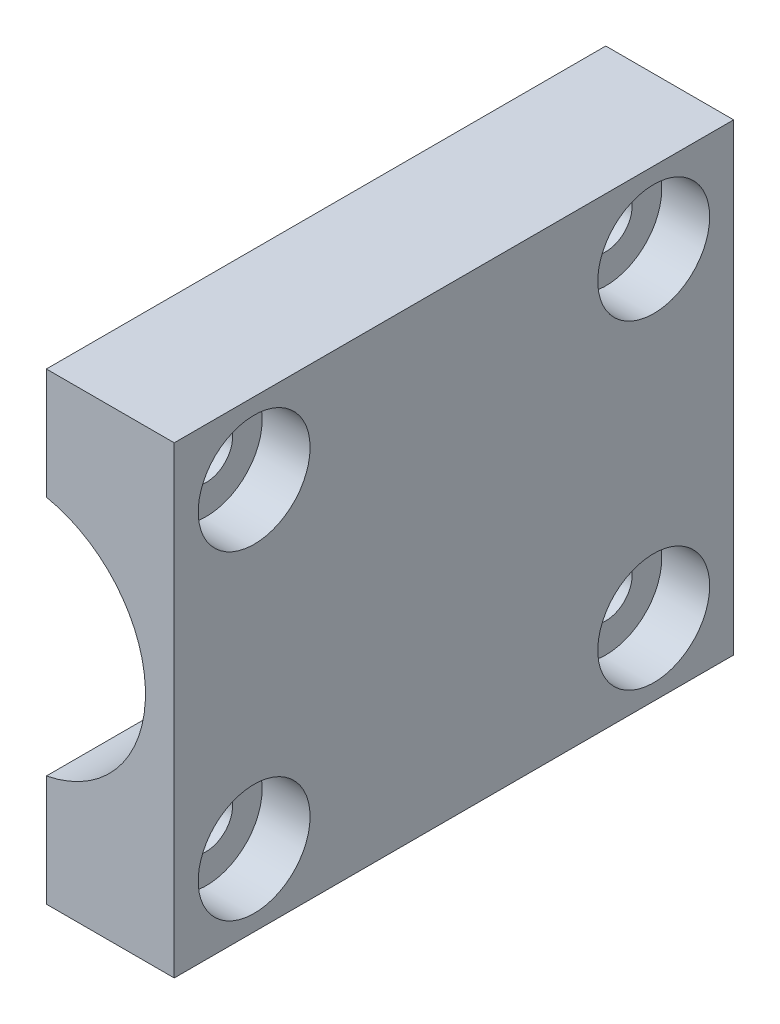
SolidWorks part; units mm, degrees
ref_plane "Plano frontal" through (0, 0, 0) normal (0, 0, 1) x (1, 0, 0)
ref_plane "Plano superior" through (0, 0, 0) normal (0, 1, 0) x (1, 0, 0)
ref_plane "Plano direito" through (0, 0, 0) normal (1, 0, 0) x (0, 0, -1)
sketch "Esboço2" plane through (0, 0, 0) normal (0, 0, 1) x (1, 0, 0)
  line L0 (-9.5, 15) -> (-9.5, 32.5)
  line L1 (-9.5, -32.5) -> (9.5, -32.5)
  line L2 (-9.5, -32.5) -> (-9.5, -15)
  line L3 (-9.5, 32.5) -> (9.5, 32.5)
  line L4 (9.5, -32.5) -> (9.5, 32.5)
  line L5 (-9.5, -32.5) -> (9.5, 32.5) construction
  line L6 (-9.5, 32.5) -> (9.5, -32.5) construction
  line L7 (-36.5, 15) -> (-9.5, 15)
  line L8 (-36.5, 15) -> (-36.5, 12)
  line L9 (-25, -15) -> (-9.5, -15)
  line L10 (0, 0) -> (-50.7474, 0) construction
  line L11 (-36.5, 15) -> (-9.5, -15) construction
  line L12 (-36.5, -15) -> (-9.5, 15) construction
  line L13 (-16, 2) -> (-9, 2)
  line L14 (-16, 2) -> (-16, 12)
  line L15 (-16, 12) -> (-9, 12)
  line L16 (-9, 2) -> (-9, 12)
  line L17 (-16, 2) -> (-9, 12) construction
  line L18 (-16, 12) -> (-9, 2) construction
  line L19 (-20.5, 12) -> (-36.5, 12)
  line L20 (-20.5, 12) -> (-20.5, 2)
  line L21 (-20.5, 2) -> (-36.5, 2)
  line L22 (-36.5, -2) -> (-25, -2)
  line L23 (-20.5, 12) -> (-36.5, 2) construction
  line L24 (-20.5, 2) -> (-36.5, 12) construction
  line L25 (-9, -2) -> (-25, -2)
  line L26 (-9, -2) -> (-9, -12)
  line L27 (-9, -12) -> (-25, -12)
  line L29 (-25, -12) -> (-25, -15)
  line L31 (-36.5, 2) -> (-36.5, -2)
  line L33 (-9, -2) -> (-25, -12) construction
  line L34 (-9, -12) -> (-25, -2) construction
  circle A0 centre (0, 0) radius 7.7
  point P7 (-23, 0)
  point P12 (-12.5, 7)
  point P18 (-28.5, 7)
  point P26 (-17, -7)
  dimension "D1" = 15.4
  dimension "D2" = 65
  dimension "D3" = 19
  dimension "D4" = 30
  dimension "D5" = 27
  dimension "D6" = 3
  dimension "D7" = 7
  dimension "D9" = 16
  dimension "D10" = 0.5
  dimension "D11" = 10
  dimension "D12" = 3
extrude "Ressalto-extrusão1" add sketch "Esboço2" along normal blind 35
sketch "Esboço3" plane through (-9.5, 0, 0) normal (-1, 0, 0) x (0, 0, 1)
  line L0 (0, 0) -> (35, 0) construction
  line L1 (35, 15) -> (0, 15) construction
  line L2 (35, 30.7367) -> (25, 32.5)
  line L3 (35, 32.5) -> (35, 15) construction
  line L4 (17.5, 32.5) -> (17.5, 15) construction
  line L5 (24.7398, 20.1694) -> (30.0578, 19.2317)
  line L6 (24.7398, 20.1694) -> (24.2189, 17.215)
  line L7 (24.2189, 17.215) -> (29.5368, 16.2773)
  line L8 (30.0578, 19.2317) -> (29.5368, 16.2773)
  line L9 (24.7398, 20.1694) -> (29.5368, 16.2773) construction
  line L10 (24.2189, 17.215) -> (30.0578, 19.2317) construction
  line L12 (19.1813, 24.7035) -> (42.7265, 20.5519) construction
  line L13 (21.3215, 23.8185) -> (42.6397, 20.0595)
  line L14 (21.4952, 24.8033) -> (42.8134, 21.0443)
  line L15 (17.5868, 25.4924) -> (42.8134, 21.0443) construction
  line L16 (17.5, 25) -> (42.7265, 20.5519) construction
  line L17 (17.4132, 24.5076) -> (42.6397, 20.0595) construction
  line L18 (42.6397, 20.0595) -> (42.8134, 21.0443)
  line L19 (19.1813, -24.7035) -> (42.7265, -20.5519) construction
  line L20 (24.2189, -17.215) -> (30.0578, -19.2317) construction
  line L21 (24.7398, -20.1694) -> (29.5368, -16.2773) construction
  line L22 (42.6397, -20.0595) -> (42.8134, -21.0443)
  line L23 (21.4952, -24.8033) -> (42.8134, -21.0443)
  line L24 (21.3215, -23.8185) -> (42.6397, -20.0595)
  line L25 (30.0578, -19.2317) -> (29.5368, -16.2773)
  line L26 (24.2189, -17.215) -> (29.5368, -16.2773)
  line L27 (24.7398, -20.1694) -> (24.2189, -17.215)
  line L28 (24.7398, -20.1694) -> (30.0578, -19.2317)
  line L29 (35, 32.5) -> (0, 32.5) construction
  line L30 (35, 15) -> (0, 15) construction
  line L31 (0, 30.7367) -> (10, 32.5)
  line L32 (0, 30.7367) -> (0, 32.5)
  line L33 (0, 32.5) -> (10, 32.5)
  line L34 (35, 30.7367) -> (35, 32.5)
  line L35 (35, 32.5) -> (25, 32.5)
  line L36 (35, -32.5) -> (25, -32.5)
  line L37 (35, -30.7367) -> (35, -32.5)
  line L38 (0, -32.5) -> (10, -32.5)
  line L39 (0, -30.7367) -> (0, -32.5)
  line L40 (0, -30.7367) -> (10, -32.5)
  line L41 (35, -30.7367) -> (25, -32.5)
  arc A0 (21.4952, 24.8033) -> (21.3215, 23.8185) centre (17.5, 25) ccw
  arc A1 (21.4952, -24.8033) -> (21.3215, -23.8185) centre (17.5, -25) cw
  circle A2 centre (17.5, 18) radius 1.65
  circle A3 centre (17.5, -18) radius 1.65
  circle A4 centre (5, 10) radius 1.65
  circle A5 centre (30, 10) radius 1.65
  circle A6 centre (5, -10) radius 1.65
  circle A7 centre (30, -10) radius 1.65
  point P11 (27.1383, 18.2234)
  point P33 (27.1383, -18.2234)
  point P37 (17.5, 32.5)
  dimension "D1" = 4
  dimension "D11" = 3.3
  dimension "D13" = 3.3
  dimension "D15" = 20
  dimension "D2" = 50
  dimension "D3" = 5.4
  dimension "D4" = 3
  dimension "D5" = 3
  dimension "D8" = 10
  dimension "D9" = 4
  dimension "D10" = 15
  dimension "D12" = 7
  dimension "D14" = 25
  dimension "D6" = 0.5
  dimension "D7" = 0.5
extrude "Corte-extrusão1" cut sketch "Esboço3" against normal through all
sketch "Esboço4" plane through (0, 15, 0) normal (0, 1, 0) x (1, 0, 0)
  line L1 (9.5, -17.5) -> (-36.5, -17.5) construction
  line L2 (9.5, -25) -> (9.5, -10) construction
  line L5 (-36.5, -35) -> (-36.5, 0) construction
  line L6 (-32, -11.5) -> (-32, -17.5) construction
  line L8 (-19, -23.5) -> (-19, -17.5) construction
  circle A0 centre (-32, -11.5) radius 1.6
  circle A1 centre (-32, -11.5) radius 5 construction
  circle A2 centre (-32, -11.5) radius 7 construction
  circle A3 centre (-19, -23.5) radius 1.6
  circle A4 centre (-19, -23.5) radius 5 construction
  dimension "D2" = 14
  dimension "D3" = 2
  dimension "D1" = 3.2
  dimension "D5" = 10
  dimension "D4" = 32
  dimension "D6" = 19
extrude "Corte-extrusão2" cut sketch "Esboço4" against normal through all both and the other way through all
sketch "Esboço8" plane through (9.5, 0, 0) normal (1, 0, 0) x (0, 0, -1)
  line L0 (-25, -32.5) -> (-10, -32.5) construction
  line L1 (-35, 32.5) -> (0, 32.5)
  line L2 (-35, 32.5) -> (-35, -32.5)
  line L3 (-35, -32.5) -> (0, -32.5)
  line L4 (0, 32.5) -> (0, -32.5)
  line L5 (-25, 32.5) -> (-10, 32.5) construction
  line L6 (-35, -21.4066) -> (-35, 21.4066) construction
  line L7 (0, -30.7367) -> (0, 30.7367) construction
extrude "Corte-extrusão4" cut sketch "Esboço8" against normal through all from offset 8 offset against normal yes
sketch "Esboço11" plane through (0, 0, 0) normal (0, 0, -1) x (-1, 0, 0)
  line L0 (-9.5, -30.7367) -> (-9.5, 30.7367) construction
  line L1 (-1.5, 32.5) -> (-9.5, 32.5)
  line L2 (-1.5, 32.5) -> (-1.5, 14.5)
  line L3 (-1.5, 14.5) -> (-9.5, 14.5)
  line L4 (-9.5, 32.5) -> (-9.5, 14.5)
  line L5 (0, 0) -> (-9.5, 0) construction
  line L6 (-1.5, -32.5) -> (-9.5, -32.5)
  line L7 (-1.5, -32.5) -> (-1.5, -14.5)
  line L8 (-1.5, -14.5) -> (-9.5, -14.5)
  line L9 (-9.5, -32.5) -> (-9.5, -14.5)
  dimension "D1" = 29
extrude "Corte-extrusão6" cut sketch "Esboço11" against normal through all both and the other way through all
sketch "Esboço12" plane through (9.5, 0, 0) normal (1, 0, 0) x (0, 0, -1)
  circle A0 centre (-30, 10) radius 3.5
  circle A1 centre (-5, 10) radius 3.5
  circle A2 centre (-5, -10) radius 3.5
  circle A3 centre (-30, -10) radius 3.5
  dimension "D1" = 7
extrude "Corte-extrusão7" cut sketch "Esboço12" against normal blind 3
